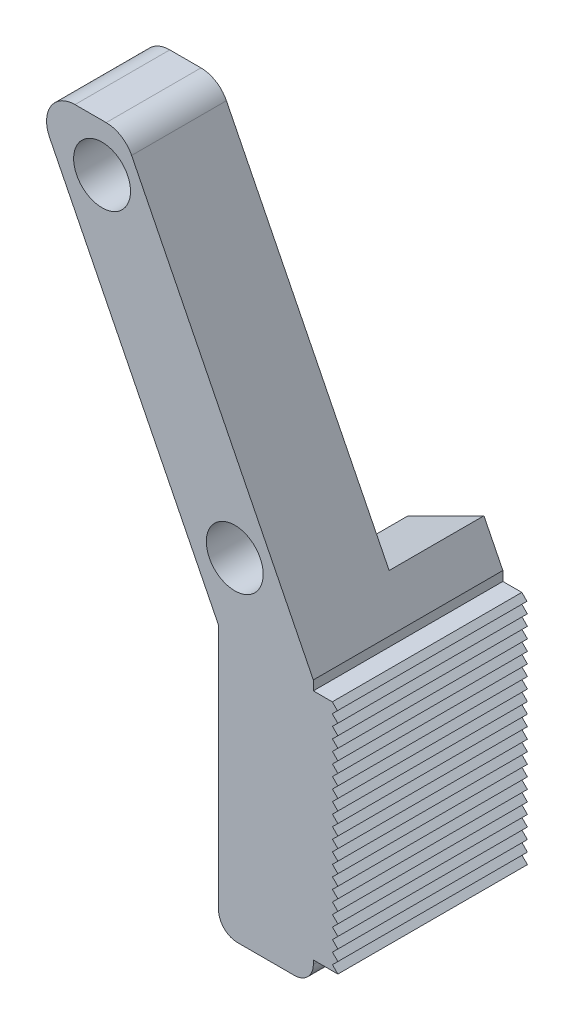
SolidWorks part; units mm, degrees
material "ABS"
ref_plane "Front Plane" through (0, 0, 0) normal (0, 0, 1) x (1, 0, 0)
ref_plane "Top Plane" through (0, 0, 0) normal (0, 1, 0) x (1, 0, 0)
ref_plane "Right Plane" through (0, 0, 0) normal (1, 0, 0) x (0, 0, -1)
sketch "Sketch2" plane through (0, 0, 0) normal (0, 0, 1) x (1, 0, 0)
  line L0 (0, 0) -> (10, -20)
  line L1 (10, -20) -> (10, -34)
  line L2 (10, -34) -> (15, -34)
  line L3 (15, -34) -> (15, -20)
  line L4 (15, -20) -> (5, 0)
  line L5 (5, 0) -> (0, 0)
  line L6 (-0.413, -13.384) -> (12.4048, -6.9751) construction
  circle A0 centre (3.855, -2.5) radius 1.5
  circle A2 centre (10.855, -16.5) radius 1.5
  dimension "D7" = 3
  dimension "D8" = 3.5
  dimension "D1" = 5
  dimension "D2" = 20
  dimension "D3" = 15
  dimension "D4" = 34
  dimension "D5" = 2.5
  dimension "D6" = 2.33
extrude "Boss-Extrude1" add sketch "Sketch2" along normal blind 10
sketch "Sketch3" plane through (0, 0, 0) normal (-0.8944, -0.4472, 0) x (0, 0, 1)
  line L0 (5, 0) -> (5, -22.3607)
  line L1 (10, 0) -> (0, 0) construction
  line L2 (10, -22.3607) -> (0, -22.3607) construction
  line L3 (10, 0) -> (10, -22.3607) construction
  line L7 (5, 0) -> (0, 0)
  line L8 (0, 0) -> (0, -22.3607)
  line L9 (0, -22.3607) -> (5, -22.3607)
  dimension "D1" = 5
extrude "Cut-Extrude1" cut sketch "Sketch3" against normal blind 10
fillet "Fillet2" radius 1.5 2 edges at (5, 0, 7.5) (0, 0, 7.5)
fillet "Fillet3" radius 1 2 edges at (15, -34, 5) (10, -34, 5)
sketch "Sketch4" plane through (0, 0, 10) normal (0, 0, 1) x (1, 0, 0)
  line L0 (15, -20.5) -> (16, -20.5)
  line L1 (15, -33) -> (15, -20) construction
  line L2 (16, -20.5) -> (16.2716, -20.7716)
  line L3 (16.2716, -20.7716) -> (16, -21.0432)
  line L4 (16, -21.0432) -> (16.2909, -21.3342)
  line L5 (16.2909, -21.3342) -> (16.0088, -21.6163)
  line L6 (16.0088, -21.6163) -> (16.2953, -21.9029)
  line L7 (16.2953, -21.9029) -> (16.0088, -22.1894)
  line L8 (16.0088, -22.1894) -> (16.2953, -22.476)
  line L9 (16.2953, -22.476) -> (16.0088, -22.7625)
  line L10 (16.0088, -22.7625) -> (16.2953, -23.0491)
  line L11 (16.2953, -23.0491) -> (16.0088, -23.3356)
  line L12 (16.0088, -23.3356) -> (16.2953, -23.6222)
  line L13 (16.2953, -23.6222) -> (16.0088, -23.9087)
  line L14 (16.0088, -23.9087) -> (16.2953, -24.1953)
  line L15 (16.2953, -24.1953) -> (16.0088, -24.4818)
  line L16 (16.0088, -24.4818) -> (16.2953, -24.7683)
  line L17 (16.2953, -24.7683) -> (16.0088, -25.0549)
  line L18 (16.0088, -25.0549) -> (16.2953, -25.3414)
  line L19 (16.2953, -25.3414) -> (16.0088, -25.628)
  line L20 (16.0088, -25.628) -> (16.2953, -25.9145)
  line L21 (16.2953, -25.9145) -> (16.0088, -26.2011)
  line L22 (16.0088, -26.2011) -> (16.2953, -26.4876)
  line L23 (16.2953, -26.4876) -> (16.0088, -26.7742)
  line L24 (16.0088, -26.7742) -> (16.2953, -27.0607)
  line L25 (16.2953, -27.0607) -> (16.0088, -27.3473)
  line L26 (16.0088, -27.3473) -> (16.2953, -27.6338)
  line L27 (16.2953, -27.6338) -> (16.0088, -27.9204)
  line L28 (16.0088, -27.9204) -> (16.2953, -28.2069)
  line L29 (16.2953, -28.2069) -> (16.0088, -28.4935)
  line L30 (16.0088, -28.4935) -> (16.2953, -28.78)
  line L31 (16.2953, -28.78) -> (16.0088, -29.0666)
  line L32 (16.0088, -29.0666) -> (16.2953, -29.3531)
  line L33 (16.2953, -29.3531) -> (16.0088, -29.6397)
  line L34 (16.0088, -29.6397) -> (16.2953, -29.9262)
  line L35 (16.2953, -29.9262) -> (16.0088, -30.2128)
  line L36 (16.0088, -30.2128) -> (16.2953, -30.4993)
  line L37 (16.2953, -30.4993) -> (16.0088, -30.7859)
  line L38 (16.0088, -30.7859) -> (16.2953, -31.0724)
  line L39 (16.2953, -31.0724) -> (16.0088, -31.359)
  line L40 (16.0088, -31.359) -> (16.2953, -31.6455)
  line L41 (16.2953, -31.6455) -> (16.0088, -31.9321)
  line L42 (16.0088, -31.9321) -> (16.2953, -32.2186)
  line L43 (16.2953, -32.2186) -> (16.0088, -32.5052)
  line L44 (16.0088, -32.5052) -> (16.2953, -32.7917)
  line L45 (16.2953, -32.7917) -> (15, -32.7917)
  line L46 (15, -32.7917) -> (15, -20.5)
  dimension "D1" = 0.5
  dimension "D2" = 135
  dimension "D3" = 0.3841
  dimension "D4" = 0.2083
  dimension "D5" = 1
extrude "Boss-Extrude2" add sketch "Sketch4" against normal up to surface (10 mm away) up to face at (12.7143, -27.4877, 0)
